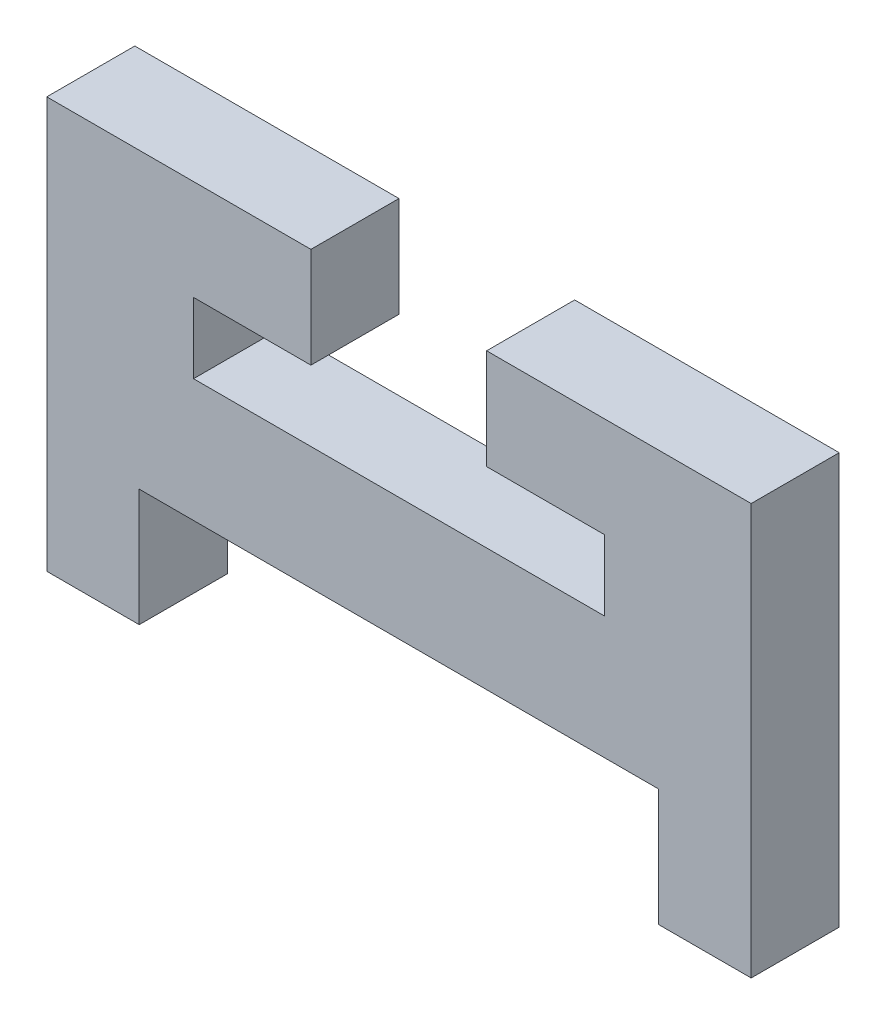
SolidWorks part; units mm, degrees
ref_plane "Alzado" through (0, 0, 0) normal (0, 0, 1) x (1, 0, 0)
ref_plane "Planta" through (0, 0, 0) normal (0, 1, 0) x (1, 0, 0)
ref_plane "Vista lateral" through (0, 0, 0) normal (1, 0, 0) x (0, 0, -1)
sketch "Model" plane through (0, 0, 0) normal (0, 0, 1) x (1, 0, 0)
  line L0 (29.5, 19.6827) -> (22, 19.6827)
  line L1 (22, 19.6827) -> (22, 22.0827)
  line L2 (22, 22.0827) -> (26, 22.0827)
  line L3 (26, 22.0827) -> (26, 25.5)
  line L4 (26, 25.5) -> (17, 25.5)
  line L5 (17, 25.5) -> (17, 11.5)
  line L6 (17, 11.5) -> (20.15, 11.5)
  line L7 (20.15, 11.5) -> (20.15, 15.5)
  line L8 (20.15, 15.5) -> (37.85, 15.5)
  line L9 (37.85, 15.5) -> (37.85, 11.5)
  line L10 (37.85, 11.5) -> (41, 11.5)
  line L11 (41, 11.5) -> (41, 25.5)
  line L12 (41, 25.5) -> (31.9864, 25.5)
  line L13 (31.9864, 25.5) -> (31.9864, 22.0827)
  line L14 (31.9864, 22.0827) -> (36, 22.0827)
  line L15 (36, 22.0827) -> (36, 19.6827)
  line L16 (36, 19.6827) -> (29.5, 19.6827)
extrude "Saliente-Extruir1" add sketch "Model" along normal blind 3
